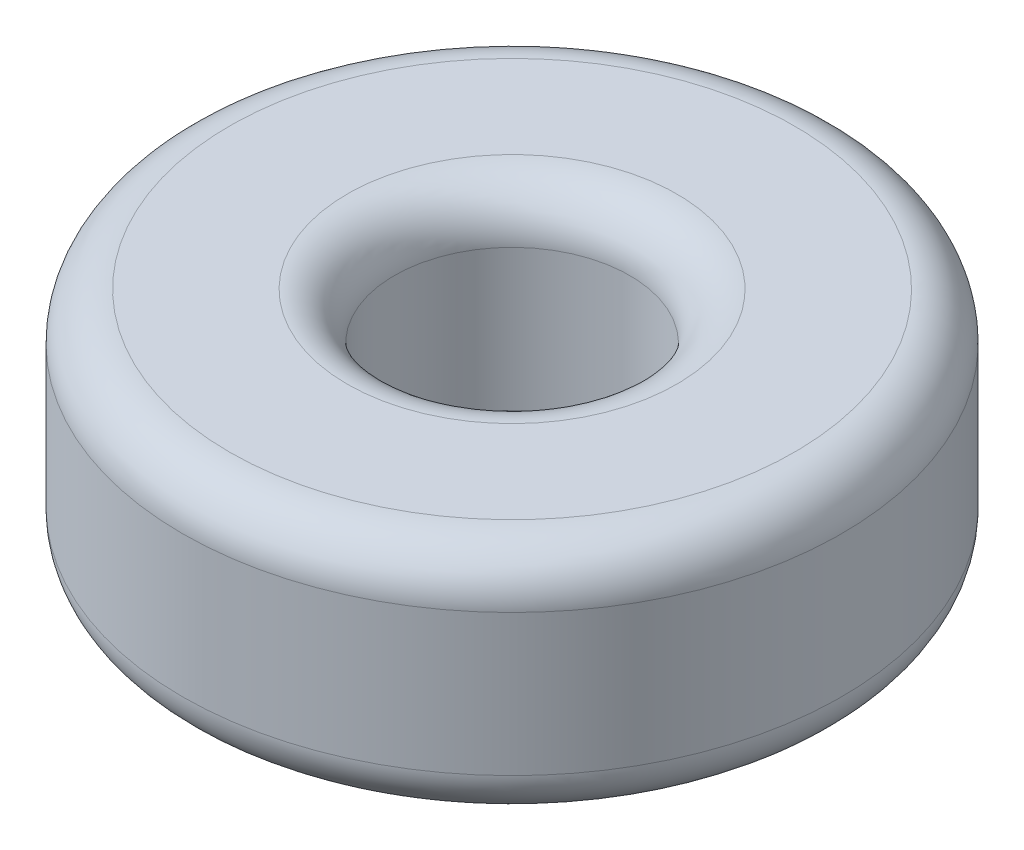
SolidWorks part; units mm, degrees
ref_plane "Front Plane" through (0, 0, 0) normal (0, 0, 1) x (1, 0, 0)
ref_plane "Top Plane" through (0, 0, 0) normal (0, 1, 0) x (1, 0, 0)
ref_plane "Right Plane" through (0, 0, 0) normal (1, 0, 0) x (0, 0, -1)
sketch "Sketch1" plane through (0, 0, 0) normal (0, 1, 0) x (1, 0, 0)
  circle A0 centre (0, 0) radius 2.5
  circle A1 centre (0, 0) radius 7
  dimension "D1" = 14
  dimension "D2" = 5
extrude "Boss-Extrude1" add sketch "Sketch1" along normal blind 5
fillet "Fillet1" radius 1 2 edges at (0, 0, 7) (0, 5, 7)
fillet "Fillet2" radius 1 2 edges at (0, 0, 2.5) (0, 5, 2.5)
